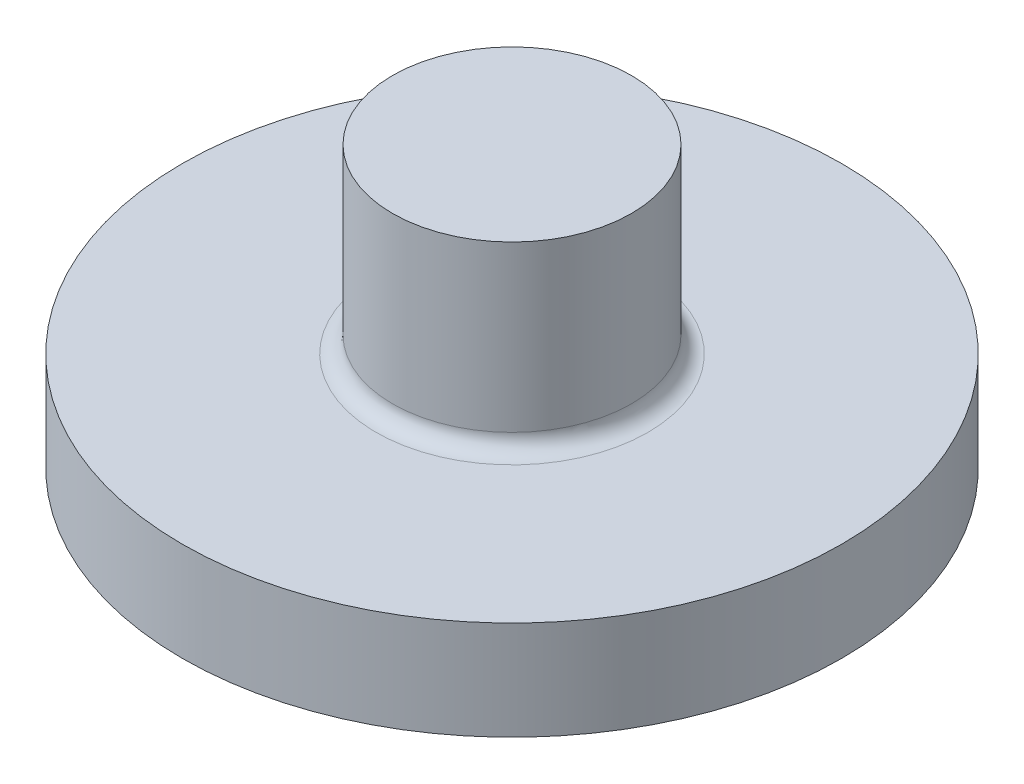
SolidWorks part; units mm, degrees
material "6061-T6 (SS)"
ref_plane "Front Plane" through (0, 0, 0) normal (0, 0, 1) x (1, 0, 0)
ref_plane "Top Plane" through (0, 0, 0) normal (0, 1, 0) x (1, 0, 0)
ref_plane "Right Plane" through (0, 0, 0) normal (1, 0, 0) x (0, 0, -1)
sketch "Sketch1" plane through (0, 0, 0) normal (0, 0, 1) x (1, 0, 0)
  line L0 (0, 48.1817) -> (0, 4.1299) construction
  line L1 (0, 1.7) -> (0.725, 1.7)
  line L2 (0.725, 1.7) -> (0.725, 0.6)
  line L3 (0.725, 0.6) -> (2, 0.6)
  line L4 (2, 0.6) -> (2, 0)
  line L5 (2, 0) -> (0, 0)
  line L6 (0, 0) -> (0, 1.7)
  dimension "D1" = 0.6
  dimension "D2" = 1.1
  dimension "D3" = 4
  dimension "D4" = 1.45
revolve "Revolve1" add sketch "Sketch1" angle 360 about L0
fillet "Fillet1" radius 0.1 1 edges at (-0.725, 0.6, 0)
